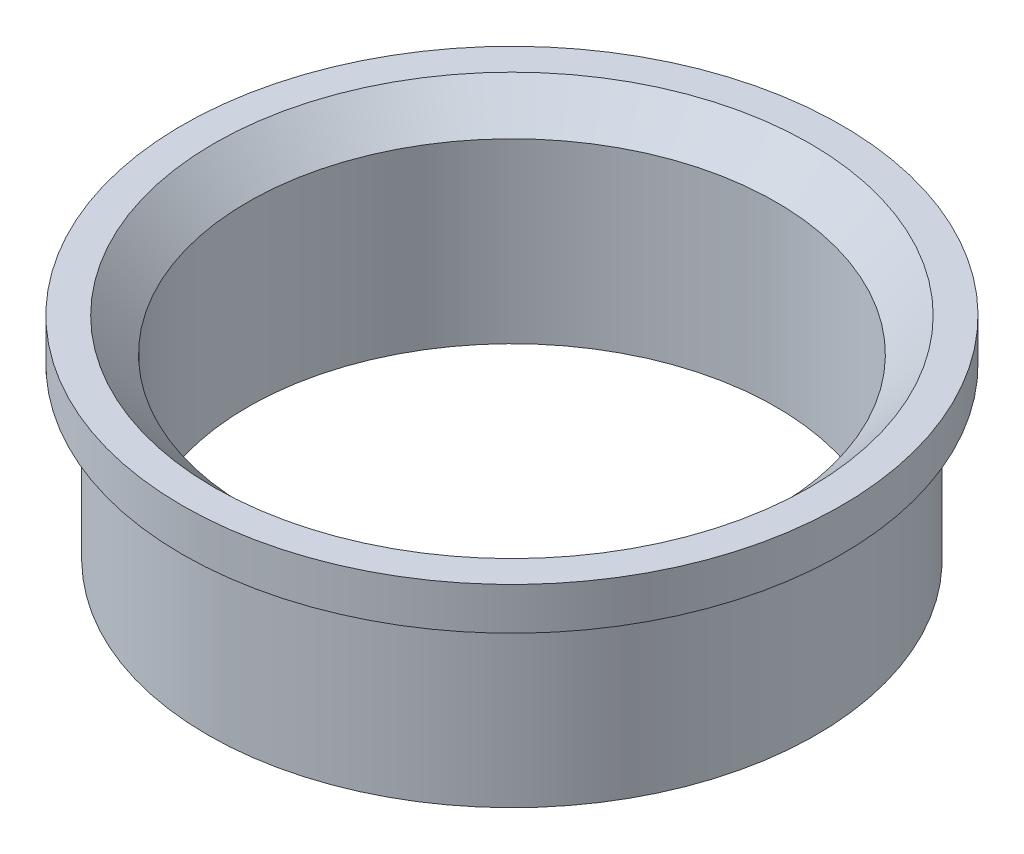
SolidWorks part; units mm, degrees
ref_plane "Front Plane" through (0, 0, 0) normal (0, 0, 1) x (1, 0, 0)
ref_plane "Top Plane" through (0, 0, 0) normal (0, 1, 0) x (1, 0, 0)
ref_plane "Right Plane" through (0, 0, 0) normal (1, 0, 0) x (0, 0, -1)
sketch "Sketch1" plane through (0, 0, 0) normal (1, 0, 0) x (0, 0, -1)
  line L0 (0, 75.2986) -> (0, -83.4044) construction
  line L1 (-187.5, 0) -> (175.9812, 0) construction
  line L2 (62.5, 0) -> (62.5, 42)
  line L3 (62.5, 42) -> (70.5, 50)
  line L4 (70.5, 50) -> (78, 50)
  line L5 (78, 50) -> (78, 40)
  line L6 (78, 40) -> (72, 40)
  line L7 (72, 40) -> (72, 0)
  line L8 (72, 0) -> (62.5, 0)
  point P7 (71.7431, 64.2197)
  point P13 (62.5, 41.0909)
  dimension "D1" = 62.5
  dimension "D2" = 72
  dimension "D3" = 78
  dimension "D4" = 40
  dimension "D5" = 10
  dimension "D6" = 135
  dimension "D7" = 8
revolve "Revolve1" add sketch "Sketch1" angle 360 about L0
